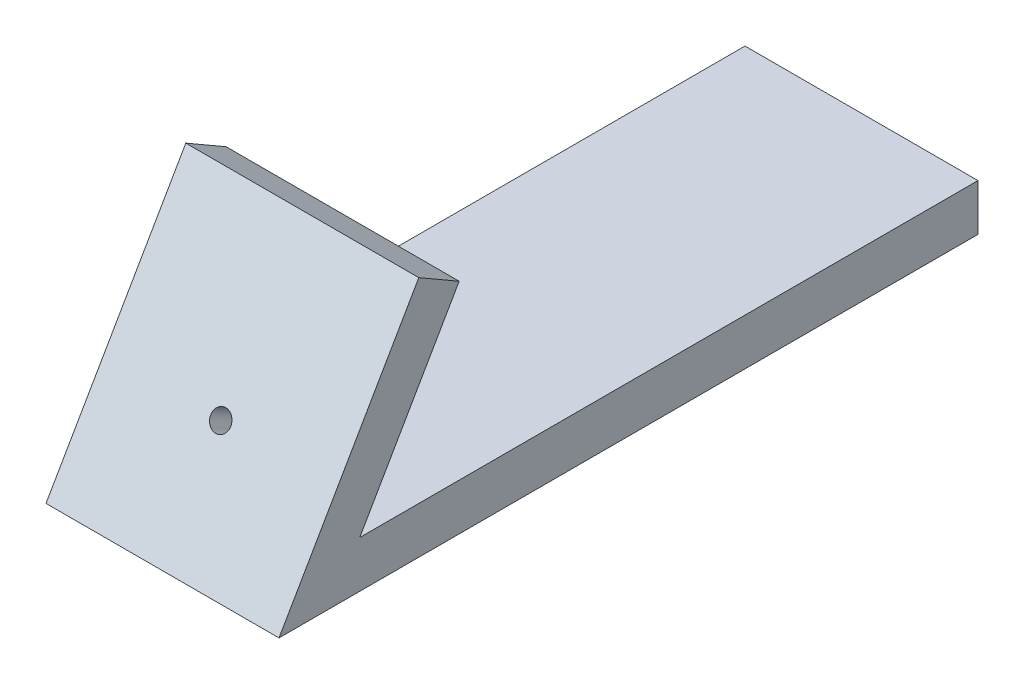
SolidWorks part; units mm, degrees
ref_plane "前视基准面" through (0, 0, 0) normal (0, 0, 1) x (1, 0, 0)
ref_plane "上视基准面" through (0, 0, 0) normal (0, 1, 0) x (1, 0, 0)
ref_plane "右视基准面" through (0, 0, 0) normal (1, 0, 0) x (0, 0, -1)
sketch "草图1" plane through (0, 0, 0) normal (1, 0, 0) x (0, 0, -1)
  line L0 (117.6963, -1.9528) -> (117.6963, -11.9528)
  line L1 (117.6963, -11.9528) -> (-32.3037, -11.9528)
  line L2 (-32.3037, -11.9528) -> (-2.3037, 40.0087)
  line L3 (-2.3037, 40.0087) -> (6.3566, 35.0087)
  line L4 (6.3566, 35.0087) -> (-14.9832, -1.9528)
  line L5 (-14.9832, -1.9528) -> (117.6963, -1.9528)
  dimension "D1" = 60
  dimension "D2" = 10
  dimension "D3" = 10
  dimension "D4" = 150
  dimension "D5" = 60
extrude "凸台-拉伸1" add sketch "草图1" along normal blind 50
sketch "草图2" plane through (0, 10.9997, 19.052) normal (0, 0.5, 0.866) x (1, 0, 0)
  line L0 (0, 33.4967) -> (0, -26.5033) construction
  line L1 (50, -26.5033) -> (0, -26.5033) construction
  circle A0 centre (25, -1.5033) radius 2.15
  dimension "D1" = 4.3
  dimension "D2" = 25
  dimension "D3" = 25
extrude "切除-拉伸1" cut sketch "草图2" against normal blind 18
